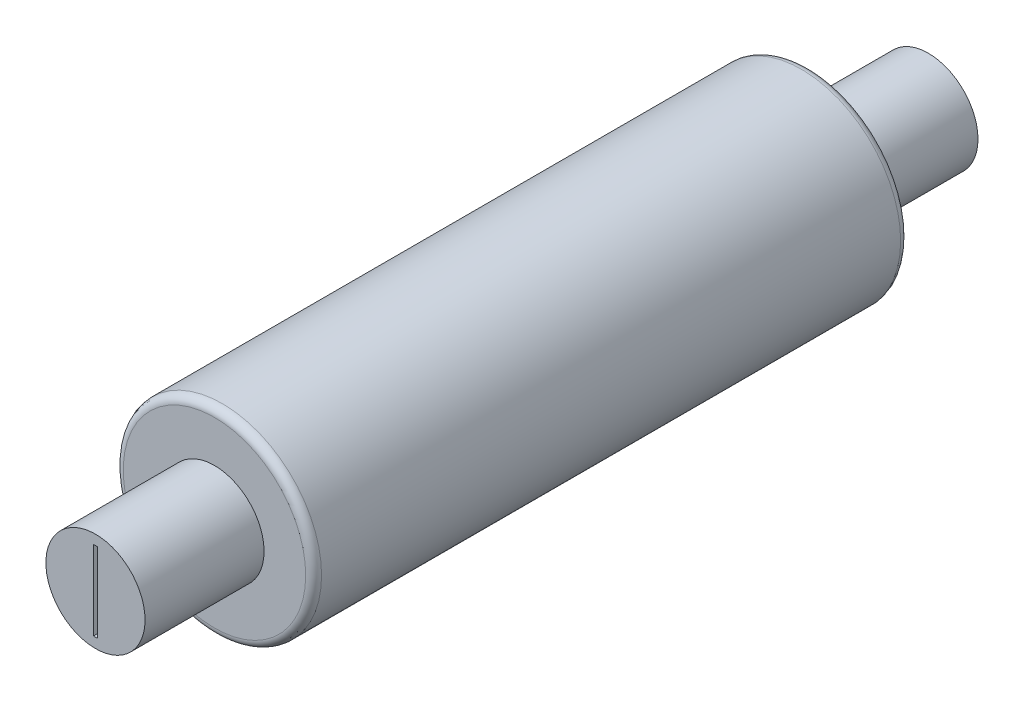
SolidWorks part; units mm, degrees
ref_plane "Front Plane" through (0, 0, 0) normal (0, 0, 1) x (1, 0, 0)
ref_plane "Top Plane" through (0, 0, 0) normal (0, 1, 0) x (1, 0, 0)
ref_plane "Right Plane" through (0, 0, 0) normal (1, 0, 0) x (0, 0, -1)
sketch "Sketch1" plane through (0, 0, 0) normal (0, 0, 1) x (1, 0, 0)
  circle A0 centre (0, 0) radius 25
  dimension "D1" = 50
extrude "Boss-Extrude2" add sketch "Sketch1" along normal mid plane 150
sketch "Sketch2" plane through (0, 0, 75) normal (0, 0, 1) x (1, 0, 0)
  line L1 (-0.5, -10) -> (0.5, -10)
  line L2 (-0.5, -10) -> (-0.5, 10)
  line L3 (-0.5, 10) -> (0.5, 10)
  line L4 (0.5, -10) -> (0.5, 10)
  line L5 (-0.5, -10) -> (0.5, 10) construction
  line L6 (-0.5, 10) -> (0.5, -10) construction
  circle A0 centre (0, 0) radius 12.5
  dimension "D1" = 25
  dimension "D2" = 20
  dimension "D3" = 1
extrude "Boss-Extrude3" add sketch "Sketch2" along normal blind 30
mirror "Mirror1" about plane through (0, 0, 0) normal (0, 0, 1) of "Boss-Extrude3"
fillet "Fillet2" radius 2 2 edges at (25, 0, -75) (25, 0, 75)
